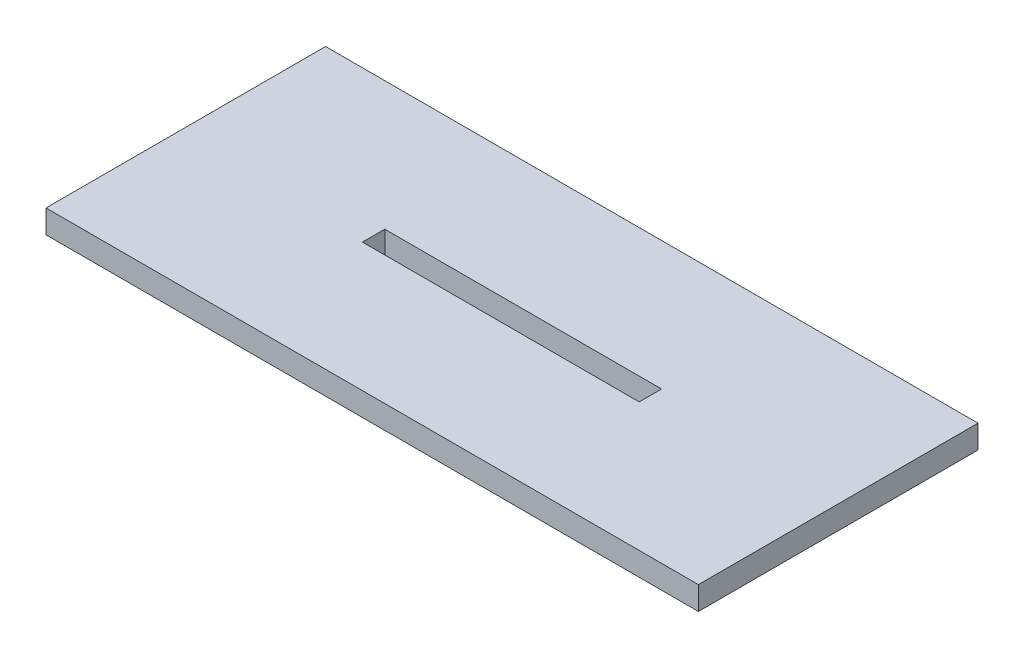
SolidWorks part; units mm, degrees
ref_plane "Front" through (0, 0, 0) normal (0, 0, 1) x (1, 0, 0)
ref_plane "Top" through (0, 0, 0) normal (0, 1, 0) x (1, 0, 0)
ref_plane "Right" through (0, 0, 0) normal (1, 0, 0) x (0, 0, -1)
sketch "Sketch1" plane through (0, 0, 0) normal (0, 1, 0) x (1, 0, 0)
  line L1 (0, 0) -> (177.8, 0)
  line L2 (0, 0) -> (0, 76.2)
  line L3 (0, 76.2) -> (177.8, 76.2)
  line L4 (177.8, 0) -> (177.8, 76.2)
  dimension "D1" = 76.2
  dimension "D2" = 177.8
extrude "Boss-Extrude1" add sketch "Sketch1" along normal blind 6.35
sketch "Sketch2" plane through (0, 6.35, 0) normal (0, 1, 0) x (-1, 0, 0)
  line L0 (0, -38.1) -> (-177.8, -38.1) construction
  line L2 (0, -76.2) -> (0, 0) construction
  line L3 (-177.8, 0) -> (-177.8, -76.2) construction
  line L5 (-51.181, -35.052) -> (-126.619, -35.052)
  line L6 (-51.181, -35.052) -> (-51.181, -41.148)
  line L7 (-51.181, -41.148) -> (-126.619, -41.148)
  line L8 (-126.619, -35.052) -> (-126.619, -41.148)
  line L9 (-51.181, -35.052) -> (-126.619, -41.148) construction
  line L10 (-51.181, -41.148) -> (-126.619, -35.052) construction
  point P6 (-88.9, -38.1)
  dimension "D1" = 75.438
  dimension "D2" = 6.096
extrude "Cut-Extrude1" cut sketch "Sketch2" against normal through all
